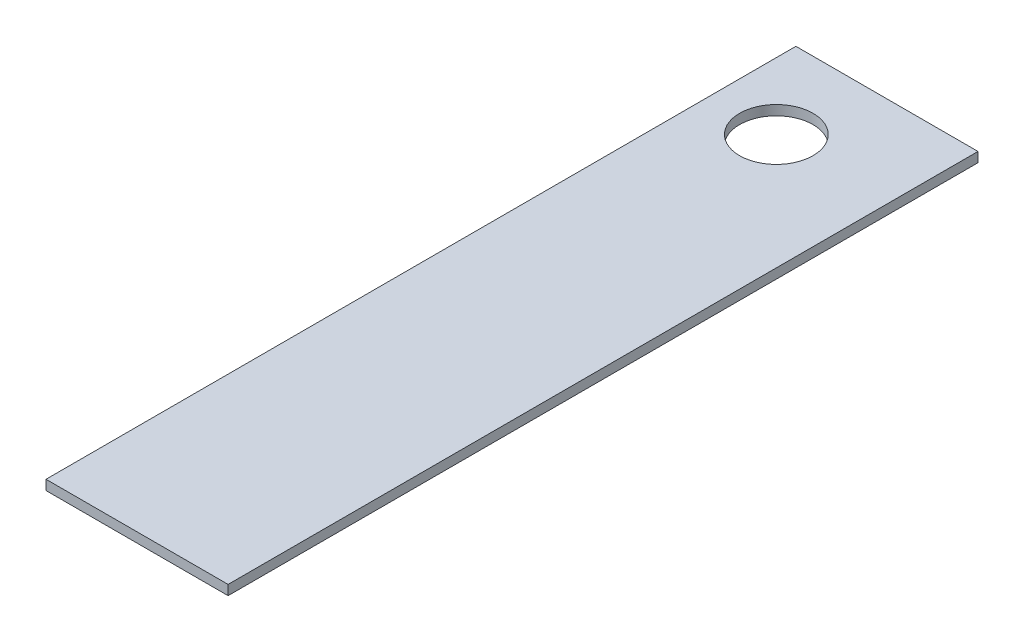
SolidWorks part; units mm, degrees
ref_plane "Front Plane" through (0, 0, 0) normal (0, 0, 1) x (1, 0, 0)
ref_plane "Top Plane" through (0, 0, 0) normal (0, 1, 0) x (1, 0, 0)
ref_plane "Right Plane" through (0, 0, 0) normal (1, 0, 0) x (0, 0, -1)
sketch "Sketch2" plane through (0, 0, 0) normal (0, 1, 0) x (1, 0, 0)
  line L1 (-41.029, -14.2823) -> (-22.429, -14.2823)
  line L2 (-41.029, -14.2823) -> (-41.029, 62.3177)
  line L3 (-41.029, 62.3177) -> (-22.429, 62.3177)
  line L4 (-22.429, -14.2823) -> (-22.429, 62.3177)
  circle A0 centre (-34.229, 53.5177) radius 3.75
  point P6 (-34.223, 52.9836)
  dimension "D5" = 7.5
  dimension "D1" = 18.6
  dimension "D2" = 76.6
  dimension "D3" = 8.8
  dimension "D4" = 6.8
extrude "Boss-Extrude1" add sketch "Sketch2" along normal blind 1
